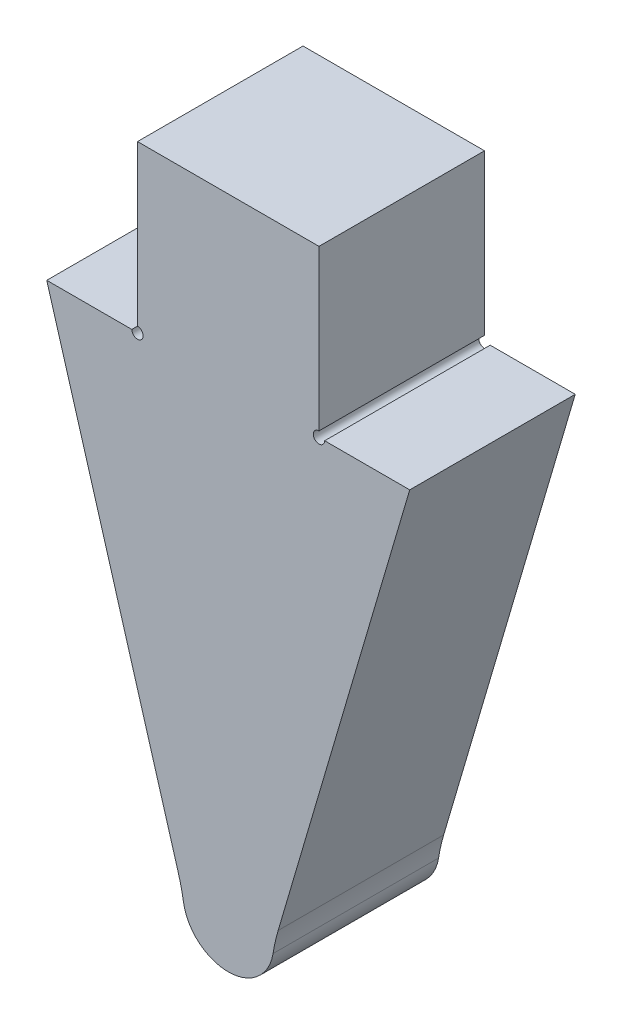
SolidWorks part; units mm, degrees
ref_plane "Front Plane" through (0, 0, 0) normal (0, 0, 1) x (1, 0, 0)
ref_plane "Top Plane" through (0, 0, 0) normal (0, 1, 0) x (1, 0, 0)
ref_plane "Right Plane" through (0, 0, 0) normal (1, 0, 0) x (0, 0, -1)
sketch "Sketch1" plane through (0, 0, 0) normal (0, 0, 1) x (1, 0, 0)
  line L0 (-3.175, 0) -> (-3.175, -17.78) construction
  line L1 (-6.35, 0) -> (-9.525, 0)
  line L2 (0, 0) -> (0, 5.7912)
  line L3 (0, 5.7912) -> (-6.35, 5.7912)
  line L4 (-6.35, 0) -> (-6.35, 5.7912)
  line L5 (3.175, 0) -> (0, 0)
  line L6 (-9.525, 0) -> (-4.7625, -16.1925)
  line L7 (3.175, 0) -> (-1.5875, -16.1925)
  arc A0 (-4.7625, -16.1925) -> (-1.5875, -16.1925) centre (-3.175, -16.1925) ccw
  point P12 (-3.175, 0)
  dimension "D1" = 6.35
  dimension "D2" = 5.7912
  dimension "D3" = 17.78
extrude "Boss-Extrude1" add sketch "Sketch1" along normal blind 5.7912
fillet "Fillet1" radius 6.35 2 edges at (-4.7625, -16.1925, 2.8956) (-1.5875, -16.1925, 2.8956)
sketch "Sketch2" plane through (0, 0, 5.7912) normal (0, 0, 1) x (1, 0, 0)
  circle A0 centre (-6.35, 0) radius 0.1984
  circle A1 centre (0, 0) radius 0.1984
  dimension "D1" = 0.3969
  dimension "D2" = 0.3969
extrude "Cut-Extrude1" cut sketch "Sketch2" against normal through all
